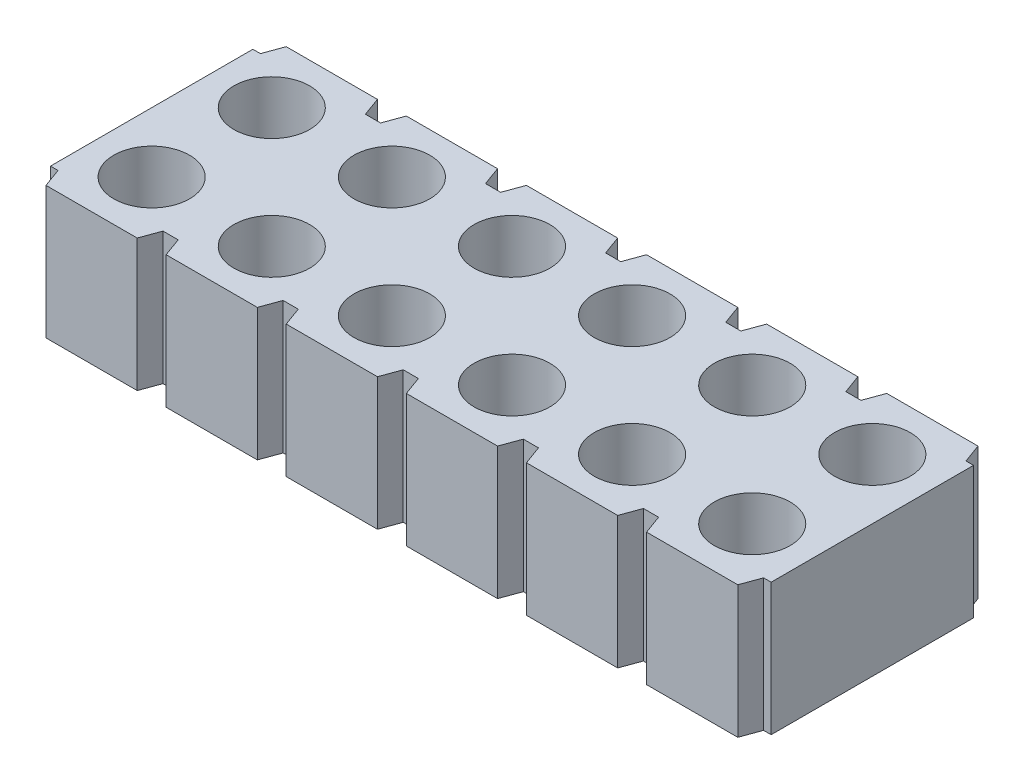
SolidWorks part; units mm, degrees
material "Nylon 46"
ref_plane "Front Plane" through (0, 0, 0) normal (0, 0, 1) x (1, 0, 0)
ref_plane "Top Plane" through (0, 0, 0) normal (0, 1, 0) x (1, 0, 0)
ref_plane "Right Plane" through (0, 0, 0) normal (1, 0, 0) x (0, 0, -1)
sketch "Sketch1" plane through (0, 0, 0) normal (0, 1, 0) x (1, 0, 0)
  line L0 (14.9344, 0.4) -> (14.7744, 0.4)
  line L1 (14.9344, 4.6799) -> (14.9344, 0.4)
  line L2 (-0.3056, 4.6799) -> (-0.1456, 4.6799)
  line L3 (-0.3056, 4.6799) -> (-0.3056, 0.4)
  line L4 (0, 0) -> (14.6287, 0)
  line L5 (0, 5.08) -> (-0.1456, 4.6799)
  line L6 (0, 0) -> (-0.1456, 0.4)
  line L7 (-0.3056, 0.4) -> (-0.1456, 0.4)
  line L9 (14.6287, 0) -> (14.7744, 0.4)
  line L10 (14.6287, 5.08) -> (14.7744, 4.6799)
  line L11 (14.9344, 4.6799) -> (14.7744, 4.6799)
  line L16 (14.6287, 5.08) -> (0, 5.08)
  dimension "D2" = 5.08
  dimension "D3" = 20
  dimension "D4" = 0.4
  dimension "D5" = 0.4
  dimension "D7" = 0.16
  dimension "INSLENGTH" = 15.24
extrude "Extrude1" add sketch "Sketch1" against normal blind 2.794
hole_wizard "Hole1" positions "3DSketch2" profile "Sketch3" legacy end condition through all
sketch3d "3DSketch2"
  line L4 (0, 0, 0) -> (14.6287, 0, 0) construction
  line L5 (-0.3056, 0, -4.6799) -> (-0.3056, 0, -0.4) construction
  point P0 (0.9644, 0, -1.27)
  dimension "D1" = 1.27
  dimension "D2" = 1.27
sketch "Sketch3" plane through (0.9644, 0, -1.27) normal (1, 0, 0) x (0, 0, 1)
  line L0 (0, 0) -> (0, 2.794)
  line L1 (0, 2.794) -> (0.8014, 2.794)
  line L2 (0.8014, 2.794) -> (0.8014, 0)
  line L3 (0.8014, 0) -> (0, 0)
  line L4 (0, 110) -> (0, -10) construction
  dimension "Diameter" = 1.6027
  dimension "Depth" = 2.794
sketch "Sketch4" plane through (0, 0, 0) normal (0, 1, 0) x (1, 0, 0)
  line L0 (1.9288, 0) -> (2.54, 0)
  line L2 (0, 0) -> (14.6287, 0) construction
  line L5 (2.0744, 0.4) -> (1.9288, 0)
  line L6 (2.3944, 0.4) -> (2.54, 0)
  line L7 (14.6287, 5.08) -> (0, 5.08) construction
  line L8 (2.0744, 0.4) -> (2.3944, 0.4)
  line L10 (2.0744, 4.6799) -> (2.3944, 4.6799)
  line L11 (2.3944, 4.6799) -> (2.54, 5.08)
  line L12 (2.0744, 4.6799) -> (1.9288, 5.08)
  line L13 (1.9288, 5.08) -> (2.54, 5.08)
  line L17 (-0.3056, 4.6799) -> (-0.3056, 0.4) construction
  dimension "D1" = 0.4
  dimension "D2" = 0.32
  dimension "D3" = 70
  dimension "D4" = 0.6112
  dimension "D5" = 0.4001
  dimension "D6" = 2.2344
extrude "Extrude2" cut sketch "Sketch4" against normal blind 2.794
pattern_linear "LPattern1" count 6 spacing 2.54 along (1, 0, 0) count 2 spacing 2.54 along (0, 0, -1) of "Hole1"
pattern_linear "LPattern2" count 35 spacing 2.54 along (1, 0, 0) of "Extrude2"
